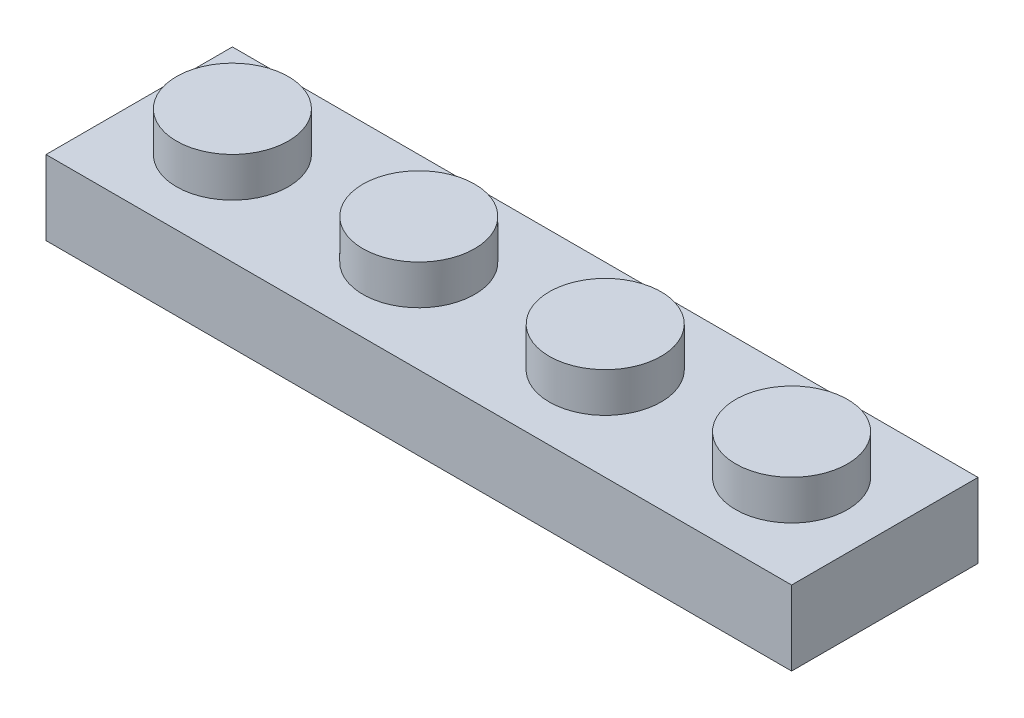
SolidWorks part; units mm, degrees
ref_plane "前基準面" through (0, 0, 0) normal (0, 0, 1) x (1, 0, 0)
ref_plane "上基準面" through (0, 0, 0) normal (0, 1, 0) x (1, 0, 0)
ref_plane "右基準面" through (0, 0, 0) normal (1, 0, 0) x (0, 0, -1)
sketch "草圖1" plane through (0, 0, 0) normal (0, 1, 0) x (1, 0, 0)
  line L1 (-4, -4) -> (4, -4)
  line L2 (-4, -4) -> (-4, 4)
  line L3 (-4, 4) -> (4, 4)
  line L4 (4, -4) -> (4, 4)
  line L5 (-4, -4) -> (4, 4) construction
  line L6 (-4, 4) -> (4, -4) construction
  point P0 (0, 0)
  dimension "width" = 8
  dimension "length" = 8
extrude "height" add sketch "草圖1" along normal blind 3.2
sketch "草圖2" plane through (0, 3.2, 0) normal (0, 1, 0) x (1, 0, 0)
  circle A0 centre (0, 0) radius 2.4
  dimension "D1" = 4.8
extrude "填料-伸長2" add sketch "草圖2" along normal blind 1.7
pattern_linear "直線複製排列1" count 4 spacing 8 along (1, 0, 0) of "填料-伸長2", "height"
shell "薄殼1" thickness 1.6
